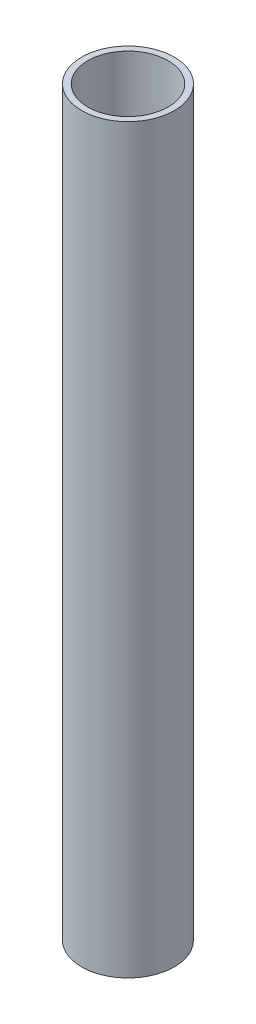
SolidWorks part; units mm, degrees
material "AISI Type 316L stainless steel"
ref_plane "Front Plane" through (0, 0, 0) normal (0, 0, 1) x (1, 0, 0)
ref_plane "Top Plane" through (0, 0, 0) normal (0, 1, 0) x (1, 0, 0)
ref_plane "Right Plane" through (0, 0, 0) normal (1, 0, 0) x (0, 0, -1)
sketch "Sketch1" plane through (0, 0, 0) normal (0, 1, 0) x (1, 0, 0)
  circle A0 centre (0, 0) radius 9.525
  circle A1 centre (0, 0) radius 8.255
  dimension "D1" = 19.05
  dimension "D2" = 1.27
extrude "Boss-Extrude1" add sketch "Sketch1" along normal blind 152.4
